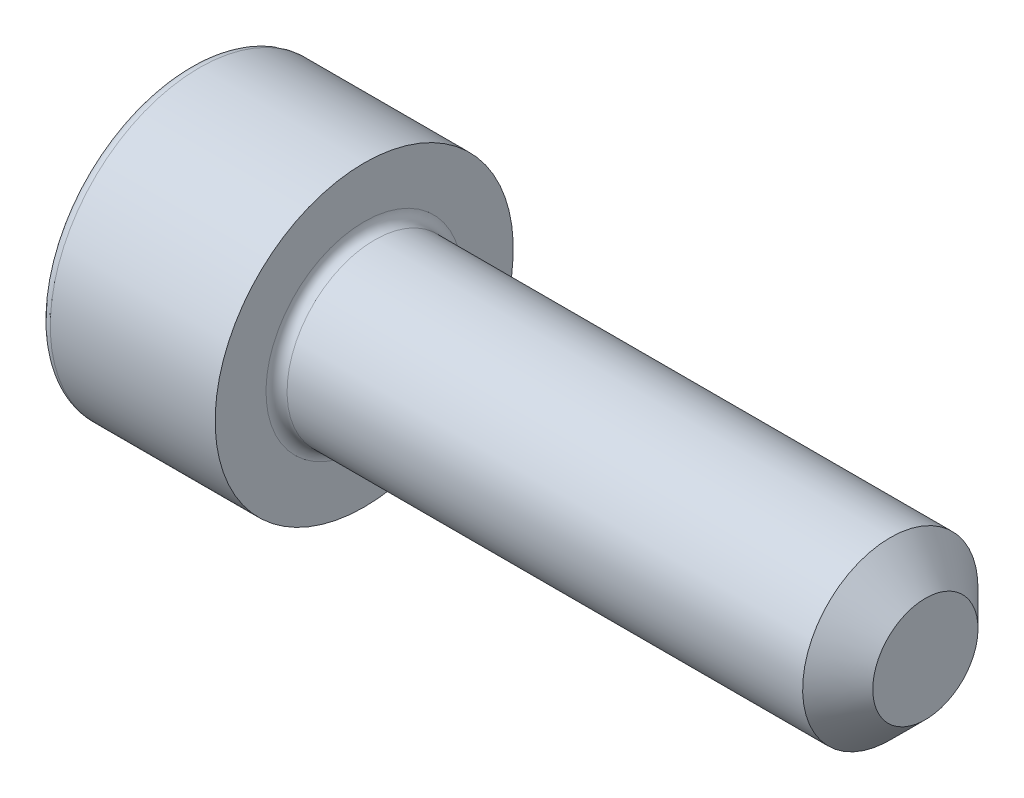
SolidWorks part; units mm, degrees
ref_plane "Спереди" through (0, 0, 0) normal (0, 0, 1) x (1, 0, 0)
ref_plane "Сверху" through (0, 0, 0) normal (0, 1, 0) x (1, 0, 0)
ref_plane "Справа" through (0, 0, 0) normal (1, 0, 0) x (0, 0, -1)
sketch "Эскиз1" plane through (0, 0, 0) normal (0, 0, 1) x (1, 0, 0)
  line L0 (0, 0) -> (0, 4.25)
  line L1 (0, 4.25) -> (5, 4.25)
  line L2 (5, 4.25) -> (5, 2.5)
  line L3 (5, 2.5) -> (21, 2.5)
  line L4 (21, 2.5) -> (21, 0)
  line L5 (21, 0) -> (0, 0) construction
  line L6 (0, 0) -> (21, 0)
  dimension "D1" = 8.5
  dimension "D2" = 5
  dimension "D3" = 5
  dimension "D4" = 16
revolve "Повернуть1" add sketch "Эскиз1" angle 360 about L5
cosmetic thread "Условное изображение резьбы1" parameters "D2"=4.11
sketch "Эскиз2" plane through (0, 0, 0) normal (-1, 0, 0) x (0, 0, 1)
  line L1 (-1.1547, 2) -> (-2.3094, 0)
  line L2 (-2.3094, 0) -> (-1.1547, -2)
  line L3 (-1.1547, -2) -> (1.1547, -2)
  line L4 (1.1547, -2) -> (2.3094, 0)
  line L5 (2.3094, 0) -> (1.1547, 2)
  line L6 (1.1547, 2) -> (-1.1547, 2)
  circle A0 centre (0, 0) radius 2 construction
  dimension "D1" = 4
extrude "Вырез-Вытянуть1" cut sketch "Эскиз2" against normal blind 2.5
fillet "Скругление1" radius 0.3 2 edges at (0, 4.25, 0) (5, 2.5, 0)
chamfer "Фаска1" distance 1 angle 45 1 edges at (21, 2.5, 0)
